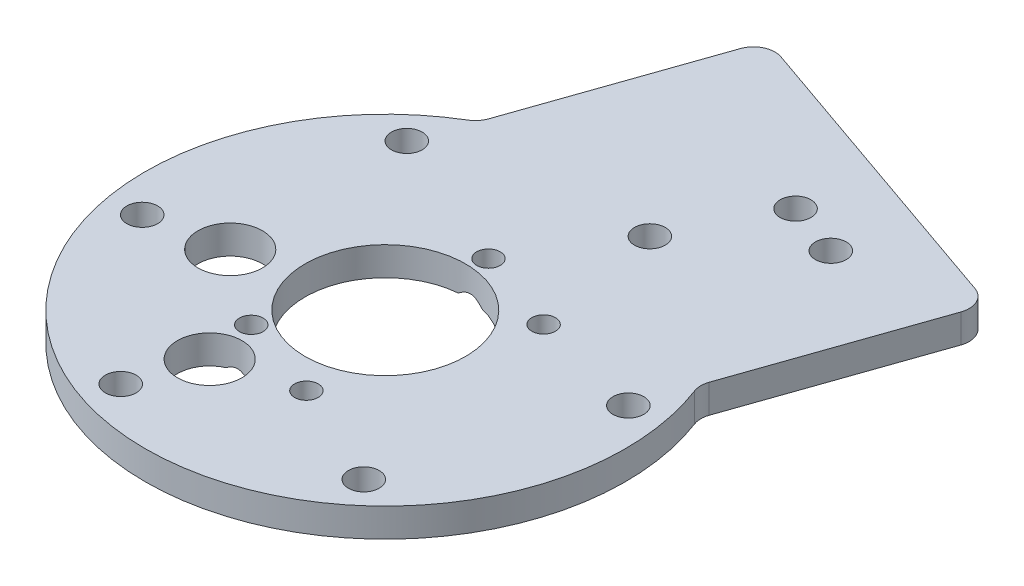
SolidWorks part; units mm, degrees
material "Thornel Mat VMA"
ref_plane "前视基准面" through (0, 0, 0) normal (0, 0, 1) x (1, 0, 0)
ref_plane "上视基准面" through (0, 0, 0) normal (0, 1, 0) x (1, 0, 0)
ref_plane "右视基准面" through (0, 0, 0) normal (1, 0, 0) x (0, 0, -1)
other "Configuration Table"
sketch "草图1" plane through (0, 0, 0) normal (0, 1, 0) x (1, 0, 0)
  circle A0 centre (0, 0) radius 33.5
  dimension "D1" = 67
extrude "凸台-拉伸1" add sketch "草图1" along normal blind 4
sketch "草图2" plane through (0, 4, 0) normal (0, 1, 0) x (1, 0, 0)
  circle A1 centre (-18.9507, 21.9516) radius 2.15
  circle A7 centre (-18.9507, 21.9516) radius 2.1 construction
  circle A8 centre (9.5353, 27.3876) radius 2.15
  circle A9 centre (28.486, 5.436) radius 2.15
  circle A10 centre (18.9507, -21.9516) radius 2.15
  circle A11 centre (-9.5353, -27.3876) radius 2.15
  circle A12 centre (-28.486, -5.436) radius 2.15
  point P17 (0, 0)
  point P18 (0, 0)
  dimension "D1" = 6
  dimension "D2" = 4.3
extrude "切除-拉伸1" cut sketch "草图2" against normal blind 24
sketch "草图3" plane through (0, 4, 0) normal (0, 1, 0) x (1, 0, 0)
  line L0 (-19.3591, -6.8502) -> (-15.8229, -6.1754) construction
  line L1 (-20.9187, -1.345) -> (-19.9439, -6.4528) construction
  line L2 (-16.9851, -0.0853) -> (-20.5213, -0.7601) construction
  line L3 (-15.4255, -5.5906) -> (-16.4002, -0.4827) construction
  line L4 (-19.3591, -6.8502) -> (-15.8229, -6.1754) construction
  line L5 (-20.9187, -1.345) -> (-19.9439, -6.4528) construction
  line L6 (-16.9851, -0.0853) -> (-20.5213, -0.7601) construction
  line L7 (-15.4255, -5.5906) -> (-16.4002, -0.4827) construction
  line L8 (-20.4275, -1.2513) -> (-15.9166, -5.6843) construction
  line L9 (-16.8913, -0.5765) -> (-19.4528, -6.3591) construction
  circle A0 centre (-18.1721, -3.4678) radius 4.5
  circle A1 centre (-6.3295, -18.1797) radius 4.5
  circle A2 centre (-6.3295, -18.1797) radius 4 construction
  arc A4 (-15.8229, -6.1754) -> (-15.4255, -5.5906) centre (-15.9166, -5.6843) ccw construction
  arc A5 (-19.9439, -6.4528) -> (-19.3591, -6.8502) centre (-19.4528, -6.3591) ccw construction
  arc A6 (-20.5213, -0.7601) -> (-20.9187, -1.345) centre (-20.4275, -1.2513) ccw construction
  arc A7 (-16.4002, -0.4827) -> (-16.5129, -0.2497) centre (-16.8913, -0.5765) ccw construction
  arc A8 (-16.5129, -0.2497) -> (-16.9851, -0.0853) centre (-16.8913, -0.5765) ccw construction
  arc A9 (-15.8229, -6.1754) -> (-15.4255, -5.5906) centre (-15.9166, -5.6843) ccw construction
  arc A10 (-19.9439, -6.4528) -> (-19.3591, -6.8502) centre (-19.4528, -6.3591) ccw construction
  arc A11 (-20.5213, -0.7601) -> (-20.9187, -1.345) centre (-20.4275, -1.2513) ccw construction
  arc A12 (-16.4002, -0.4827) -> (-16.5129, -0.2497) centre (-16.8913, -0.5765) ccw construction
  arc A13 (-16.5129, -0.2497) -> (-16.9851, -0.0853) centre (-16.8913, -0.5765) ccw construction
  point P6 (-18.1721, -3.4678)
  dimension "D1" = 9
extrude "切除-拉伸2" cut sketch "草图3" against normal through all
sketch "草图4" plane through (0, 4, 0) normal (0, 1, 0) x (1, 0, 0)
  circle A0 centre (0, 0) radius 11.2
  dimension "D1" = 22.4
extrude "切除-拉伸3" cut sketch "草图4" against normal through all
sketch "草图5" plane through (0, 0, 0) normal (0, -1, 0) x (1, 0, 0)
  circle A0 centre (12.774, -9.318) radius 1.25 construction
  circle A1 centre (0.969, -13.428) radius 1.25 construction
  circle A3 centre (4.2251, 15.2364) radius 1.25 construction
  circle A4 centre (-7.5798, 11.1264) radius 1.25 construction
  point P0 (4.2251, 15.2364)
  point P1 (12.774, -9.318)
  point P2 (0.969, -13.428)
  point P7 (-7.5798, 11.1264)
hole_wizard "孔1" positions "3D草图1" profile "草图6" legacy end condition through all
sketch3d "3D草图1"
  point P0 (12.774, 0, -9.318)
  point P3 (0.969, 0, -13.428)
  point P6 (4.2251, 0, 15.2364)
  point P9 (-7.5798, 0, 11.1264)
sketch "草图6" plane through (12.774, 0, -9.318) normal (1, 0, 0) x (0, 0, -1)
  line L0 (0, 0) -> (0, 4)
  line L1 (0, 4) -> (1.65, 4)
  line L2 (1.65, 4) -> (1.65, 1.35)
  line L3 (1.65, 1.35) -> (3, 0)
  line L4 (3, 0) -> (0, 0)
  line L5 (0, -6.4453) -> (0, 115.525) construction
  line L6 (-1.65, 1.35) -> (-3, 0) construction
  dimension "直径" = 3.3
  dimension "深度" = 4
  dimension "锥坑角度" = 90
  dimension "锥坑直径" = 6
sketch "草图9" plane through (0, 0, 0) normal (0, -1, 0) x (1, 0, 0)
  line L0 (-23.61, -8.2201) -> (-5.8546, -59.2176)
  line L1 (-5.8546, -59.2176) -> (41.3653, -42.7774)
  line L2 (41.3653, -42.7774) -> (23.61, 8.2201)
  line L3 (23.61, 8.2201) -> (-23.61, -8.2201)
  line L4 (0.969, -13.428) -> (12.774, -9.318) construction
  circle A0 centre (0, 0) radius 33.5 construction
  circle A1 centre (0, 0) radius 33.5
  point P9 (0, 0)
  circle M5 centre (4.2251, 15.2364) radius 3
  arc M6 (-4.7448, 10.1453) -> (2.5818, -10.8984) centre (0, 0) cw
  arc M8 (-0.9902, -11.1561) -> (-7.7045, 8.129) centre (0, 0) cw
  arc M9 (-7.7045, 8.129) -> (-8.1614, 14.0695) centre (-7.5798, 11.1264) cw
  arc M10 (-8.1614, 14.0695) -> (-6.022, 13.6902) centre (-6.3295, 18.1797) cw
  arc M11 (-6.022, 13.6902) -> (-4.7448, 10.1453) centre (-7.5798, 11.1264) cw
  circle M12 centre (-18.1721, 3.4678) radius 4.5
  circle M13 centre (-28.486, 5.436) radius 2.15
  circle M14 centre (-9.5353, 27.3876) radius 2.15
  circle M15 centre (18.9507, 21.9516) radius 2.15
  circle M16 centre (28.486, -5.436) radius 2.15
  circle M18 centre (-18.9507, -21.9516) radius 2.15
  circle M19 centre (0, 0) radius 33.5
  dimension "D1" = 50
  dimension "D2" = 54
extrude "凸台-拉伸2" add sketch "草图9" against normal up to surface (4 mm away) contours L1 L2 L0 M19 | L3 L2 L0 M16 M19 M18 M8 M9 M10 M11 M6 M5 M13 M15 M14 M12 up to face at (12.774, 4, -10.968)
sketch "草图10" plane through (0, 0, 0) normal (0, -1, 0) x (1, 0, 0)
  line L0 (-5.8546, -59.2176) -> (41.3653, -42.7774) construction
  line L1 (16.3561, -40.8959) -> (23.9113, -38.2655) construction
  line L2 (41.3653, -42.7774) -> (30.942, -12.8392) construction
  circle A0 centre (16.3561, -40.8959) radius 2.15
  circle A1 centre (23.9113, -38.2655) radius 2.15
  dimension "D1" = 4.3
  dimension "D2" = 8
  dimension "D3" = 10
  dimension "D4" = 15
extrude "切除-拉伸4" cut sketch "草图10" against normal up to surface (4 mm away) up to face at (28.486, 4, -3.286)
fillet "圆角1" radius 3 4 edges at (30.942, 2, -12.8392) (41.3653, 2, -42.7774) (-5.8546, 2, -59.2176) (-16.278, 2, -29.2793)
